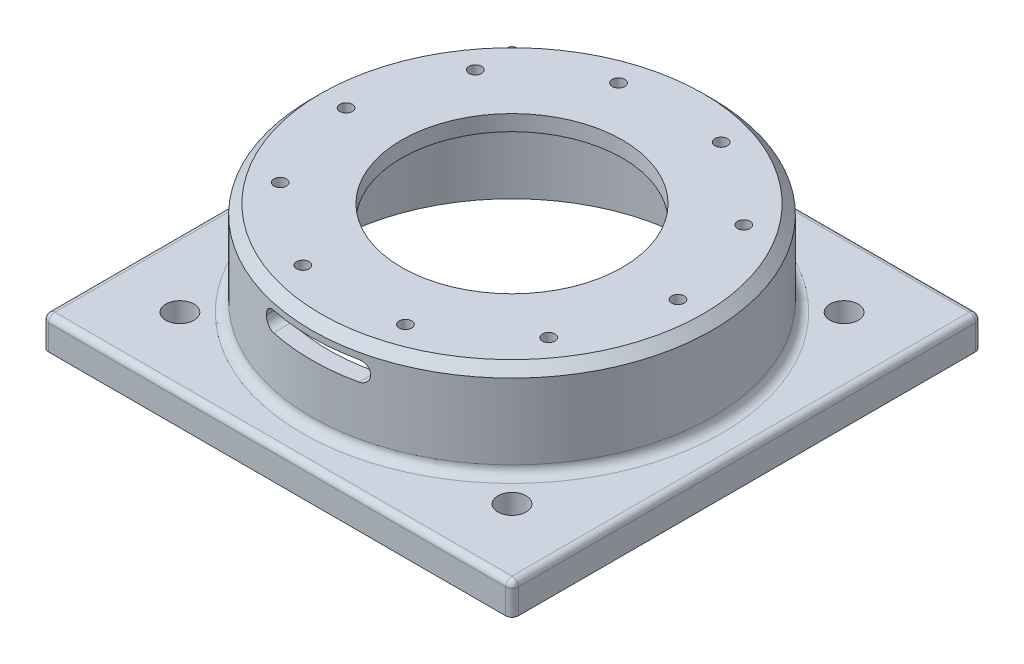
SolidWorks part; units mm, degrees
other "Камера1"
ref_plane "Спереди" through (0, 0, 0) normal (0, 0, 1) x (1, 0, 0)
ref_plane "Сверху" through (0, 0, 0) normal (0, 1, 0) x (1, 0, 0)
ref_plane "Справа" through (0, 0, 0) normal (1, 0, 0) x (0, 0, -1)
sketch "Эскиз1" plane through (0, 0, 0) normal (0, 1, 0) x (1, 0, 0)
  line L0 (0, 0) -> (53.033, 53.033) construction
  line L5 (75, -75) -> (-75, -75)
  line L6 (75, -75) -> (75, 75)
  line L7 (75, 75) -> (-75, 75)
  line L8 (-75, -75) -> (-75, 75)
  line L9 (75, -75) -> (-75, 75) construction
  line L10 (75, 75) -> (-75, -75) construction
  circle A2 centre (0, 0) radius 75 construction
  circle A3 centre (53.033, 53.033) radius 4.5
  circle A4 centre (0, 0) radius 75 construction
  circle A5 centre (53.033, -53.033) radius 4.5
  circle A6 centre (0, 0) radius 75 construction
  circle A7 centre (-53.033, -53.033) radius 4.5
  circle A8 centre (0, 0) radius 75 construction
  circle A9 centre (-53.033, 53.033) radius 4.5
  point P0 (0, 0)
  dimension "D3" = 150
  dimension "D4" = 9
  dimension "D1" = 150
  dimension "D2" = 150
  dimension "D5" = 4
extrude "Бобышка-Вытянуть1" add sketch "Эскиз1" along normal blind 10
fillet "Скругление1" radius 2 4 edges at (-75, 5, -75) (75, 5, -75) (-75, 5, 75) (75, 5, 75)
fillet "Скругление2" radius 2 8 edges at (-74.4142, 10, -74.4142) (74.4142, 10, -74.4142) (74.4142, 10, 74.4142) (-74.4142, 10, 74.4142) (0, 10, 75) (75, 10, 0) (0, 10, -75) (-75, 10, 0)
sketch "Эскиз4" plane through (0, 10, 0) normal (0, 1, 0) x (1, 0, 0)
  circle A0 centre (0, 0) radius 64
  dimension "D1" = 128
extrude "Бобышка-Вытянуть4" add sketch "Эскиз4" along normal blind 30 contours A0
fillet "Скругление5" radius 3 1 edges at (0, 10, 64)
sketch "Эскиз10" plane through (0, 0, 0) normal (0, -1, 0) x (1, 0, 0)
  circle A0 centre (0, 0) radius 58.5
  dimension "D1" = 117
sketch "Эскиз3" plane through (0, 10, 0) normal (0, 1, 0) x (1, 0, 0)
  line L0 (0, -75) -> (0, 75)
  line L1 (-73, 75) -> (73, 75) construction
  circle A1 centre (-53.033, 53.033) radius 6.25
  circle A2 centre (-53.033, -53.033) radius 6.25
  circle A3 centre (53.033, -53.033) radius 6.25
  circle A4 centre (53.033, 53.033) radius 6.25
  point P14 (0, 0)
  dimension "D2" = 12.5
  dimension "D3" = 12.5
  dimension "D1" = 150
extrude "Вырез-Вытянуть1" [suppressed] cut sketch "Эскиз3" along normal up to next contours A3 | A2 | A1 | A4
sketch "Эскиз11" plane through (0, 40, 0) normal (0, 1, 0) x (1, 0, 0)
  circle A0 centre (0, 0) radius 35.25
  dimension "D1" = 70.5
extrude "Вырез-Вытянуть2" cut sketch "Эскиз11" against normal through all contours A0
extrude "Вырез-Вытянуть3" cut sketch "Эскиз10" against normal blind 35 contours A0
sketch "Эскиз12" plane through (0, 40, 0) normal (0, 1, 0) x (1, 0, 0)
  line L0 (0, 0) -> (-53, 0) construction
  circle A0 centre (0, 0) radius 53 construction
  circle A1 centre (-53, 0) radius 2
  circle A2 centre (0, 0) radius 53
  circle A3 centre (0, 0) radius 35.25 construction
  circle A4 centre (-42.8779, 31.1526) radius 2
  circle A5 centre (0, 0) radius 53
  circle A6 centre (-16.3779, 50.406) radius 2
  circle A7 centre (0, 0) radius 53
  circle A8 centre (16.3779, 50.406) radius 2
  circle A9 centre (0, 0) radius 53
  circle A10 centre (42.8779, 31.1526) radius 2
  circle A11 centre (0, 0) radius 53
  circle A12 centre (53, 0) radius 2
  circle A13 centre (0, 0) radius 53
  circle A14 centre (42.8779, -31.1526) radius 2
  circle A15 centre (0, 0) radius 53
  circle A16 centre (16.3779, -50.406) radius 2
  circle A17 centre (0, 0) radius 53
  circle A18 centre (-16.3779, -50.406) radius 2
  circle A19 centre (0, 0) radius 53
  circle A20 centre (-42.8779, -31.1526) radius 2
  dimension "D2" = 4
  dimension "D3" = 53
  dimension "D5" = 53
  dimension "D4" = 10
extrude "Вырез-Вытянуть4" cut sketch "Эскиз12" against normal through all contours A4 | A1 | A20 | A18 | A16 | A14 | A12 | A10 | A8 | A6
chamfer "Фаска2" distance 3 angle 45 1 edges at (0, 40, 64)
ref_plane "Смещенная плоскость для разъема" through (0, 0, 64) normal (0, 0, 1) x (1, 0, 0)
sketch "Эскиз14" plane through (0, 0, 64) normal (0, 0, 1) x (1, 0, 0)
  line L0 (61, 40) -> (-61, 40) construction
  line L1 (16.625, 28.75) -> (-16.625, 28.75)
  line L2 (16.625, 28.75) -> (16.625, 35)
  line L3 (16.625, 35) -> (-16.625, 35)
  line L4 (-16.625, 28.75) -> (-16.625, 35)
  line L5 (16.625, 28.75) -> (-16.625, 35) construction
  line L6 (16.625, 35) -> (-16.625, 28.75) construction
  line L7 (-64, 37) -> (-64, 13) construction
  point P0 (0, 31.875)
  dimension "D1" = 33.25
  dimension "D2" = 6.25
  dimension "D3" = 5
  dimension "D4" = 47.375
extrude "Вырез-Вытянуть5" cut sketch "Эскиз14" against normal blind 9
fillet "Скругление7" radius 3 4 edges at (-16.625, 35, 58.9455) (-16.625, 28.75, 58.9455) (16.625, 35, 58.9455) (16.625, 28.75, 58.9455)
equation "\"D2@Эскиз1\"=\"D1@Эскиз1\""
equation "\"D3@Эскиз1\"=\"D1@Эскиз1\""
equation "\"D3@Эскиз3\"=\"D2@Эскиз3\""
